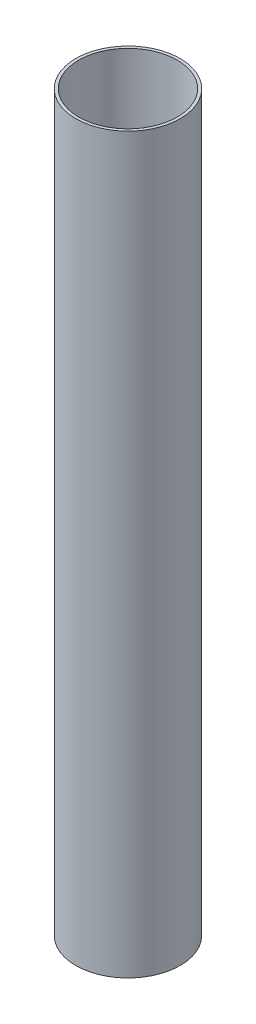
SolidWorks part; units mm, degrees
ref_plane "Front Plane" through (0, 0, 0) normal (0, 0, 1) x (1, 0, 0)
ref_plane "Top Plane" through (0, 0, 0) normal (0, 1, 0) x (1, 0, 0)
ref_plane "Right Plane" through (0, 0, 0) normal (1, 0, 0) x (0, 0, -1)
sketch "Sketch2" plane through (0, 0, 0) normal (0, 1, 0) x (1, 0, 0)
  circle A0 centre (0, 0) radius 27.3304
  circle A1 centre (0, 0) radius 28.9052
  dimension "D1" = 54.6608
  dimension "D2" = 1.5748
extrude "Boss-Extrude1" add sketch "Sketch2" along normal blind 406.4
